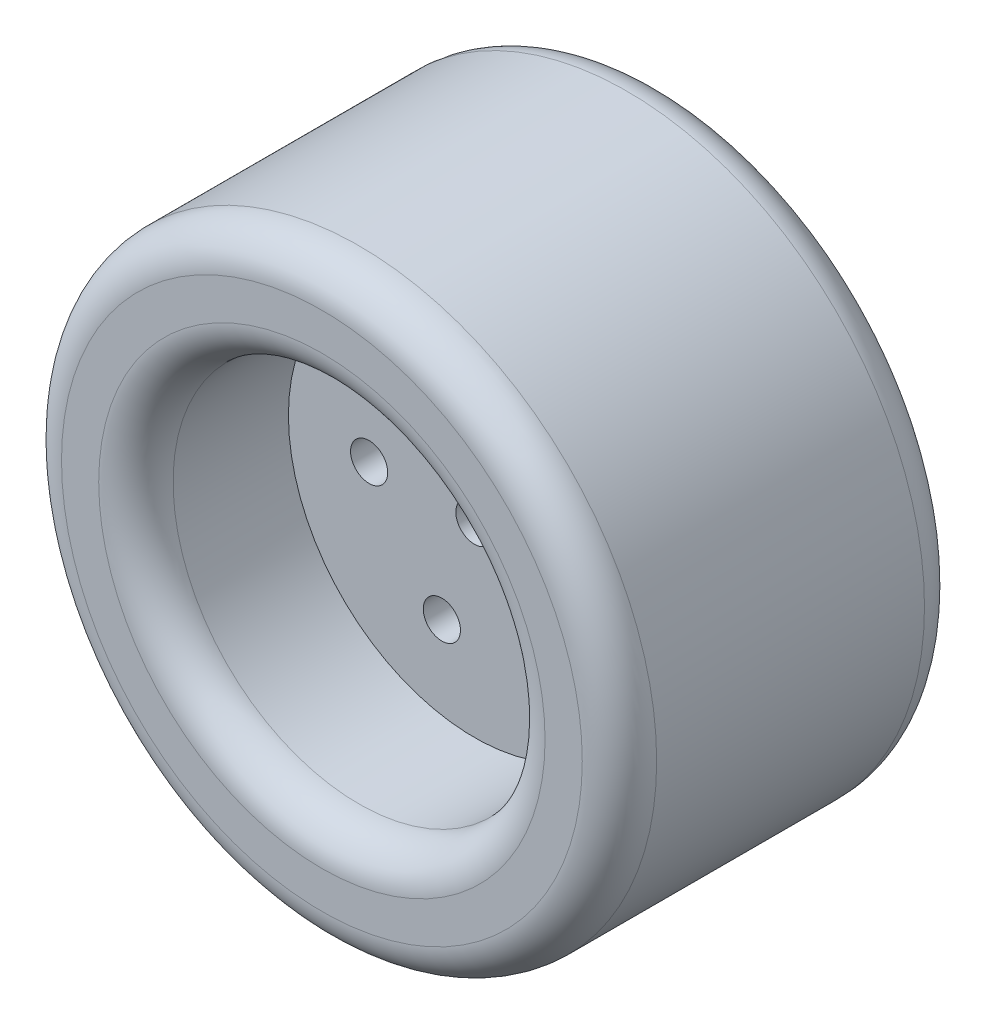
SolidWorks part; units mm, degrees
ref_plane "Front Plane" through (0, 0, 0) normal (0, 0, 1) x (1, 0, 0)
ref_plane "Top Plane" through (0, 0, 0) normal (0, 1, 0) x (1, 0, 0)
ref_plane "Right Plane" through (0, 0, 0) normal (1, 0, 0) x (0, 0, -1)
sketch "Sketch2" plane through (0, 0, 0) normal (0, 0, 1) x (1, 0, 0)
  circle A0 centre (0, 0) radius 101.6
  circle A1 centre (0, 0) radius 63.5
  dimension "D1" = 203.2
  dimension "D2" = 127
extrude "Boss-Extrude1" add sketch "Sketch2" along normal blind 114.3 and the other way blind 2.54
fillet "Fillet1" radius 12.7 4 edges at (63.5, 0, -2.54) (63.5, 0, 114.3) (101.6, 0, 114.3) (101.6, 0, -2.54)
ref_plane "Plane1" through (0, 0, 55.88) normal (0, 0, -1) x (-1, 0, 0)
sketch "Sketch4" plane through (0, 0, 55.88) normal (0, 0, -1) x (-1, 0, 0)
  line L0 (0, 0) -> (63.5, 0) construction
  circle A0 centre (0, 0) radius 63.5
  circle A1 centre (0, 0) radius 38.1 construction
  point P5 (38.1, 0)
  dimension "D1" = 127
  dimension "D2" = 76.2
extrude "Boss-Extrude2" add sketch "Sketch4" along normal blind 6.35 and the other way blind 6.35
ref_plane "Plane2" through (0, 0, 64.77) normal (0, 0, 1) x (1, 0, 0)
sketch "Sketch13" plane through (0, 0, 64.77) normal (0, 0, 1) x (1, 0, 0)
  circle A1 centre (0, 0) radius 6.35
  circle A2 centre (-35.941, 0) radius 6.35
  circle A3 centre (-11.1064, 34.1819) radius 6.35
  circle A4 centre (29.0769, 21.1256) radius 6.35
  circle A5 centre (29.0769, -21.1256) radius 6.35
  circle A6 centre (-11.1064, -34.1819) radius 6.35
  point P1 (0, 0)
  point P8 (0, 0)
  point P9 (0, 0)
  point P17 (0, 0)
  dimension "D3" = 5
extrude "Cut-Extrude1" cut sketch "Sketch13" against normal through all and the other way through all contours A1 | A2 | A3 | A4 | A5 | A6
